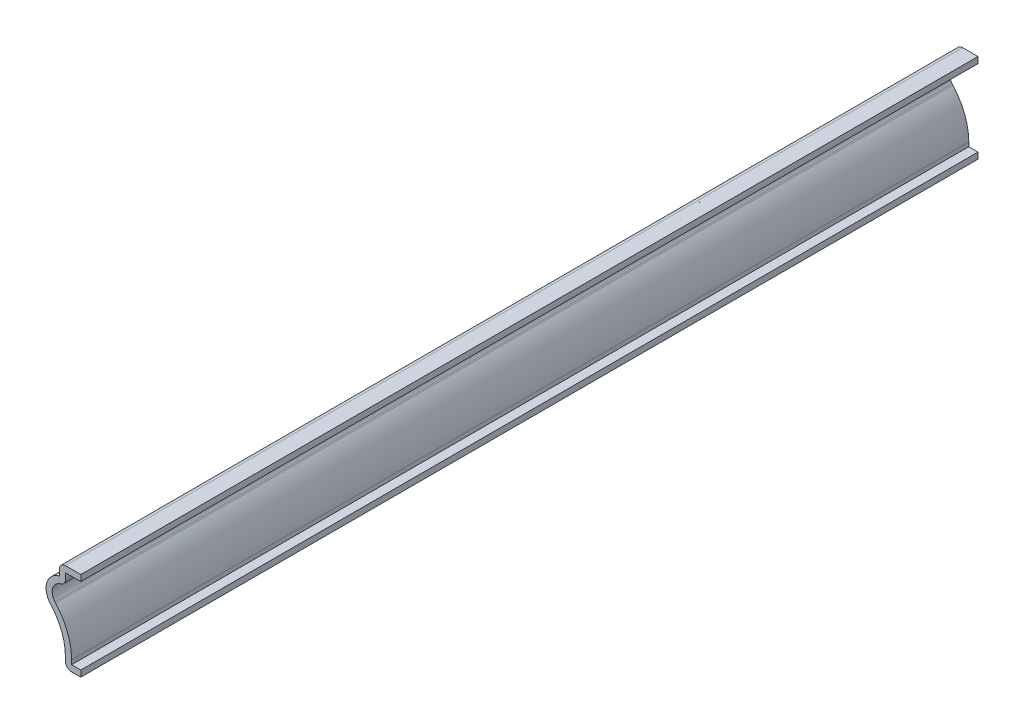
SolidWorks part; units mm, degrees
ref_plane "Front Plane" through (0, 0, 0) normal (0, 0, 1) x (1, 0, 0)
ref_plane "Top Plane" through (0, 0, 0) normal (0, 1, 0) x (1, 0, 0)
ref_plane "Right Plane" through (0, 0, 0) normal (1, 0, 0) x (0, 0, -1)
sketch "Sketch1" plane through (0, 0, 0) normal (0, 0, 1) x (1, 0, 0)
  line L0 (-28.8706, -7.969) -> (13.3286, -7.969) construction
  line L1 (-7.1437, 16.9659) -> (-7.1437, 7.0241) construction
  line L3 (0, 18.2562) -> (0, 0) construction
  line L6 (-3.1637, 0) -> (-3.1637, 2.1195)
  line L7 (-4.4218, 18.2562) -> (-4.4218, 15.7747)
  line L8 (0, 18.2562) -> (-4.4218, 18.2562)
  line L9 (0, 0) -> (-3.1637, 0)
  arc A3 (-6.101, 9.7262) -> (-6.2847, 9.9354) centre (0.1694, 15.4172) cw
  arc A4 (-6.2847, 9.9354) -> (-4.4218, 15.7747) centre (-3.5315, 12.2738) cw
  arc A5 (-3.1637, 2.1195) -> (-6.101, 9.7262) centre (-14.482, 2.1195) ccw
extrude "Extrude-Thin1" add sketch "Sketch1" against normal blind 184.15 thin
fillet "Fillet1" radius 1.27 3 edges at (-3.1637, 0, -92.075) (-3.1518, 14.5852, -92.075) (-4.4218, 18.2562, -92.075)
